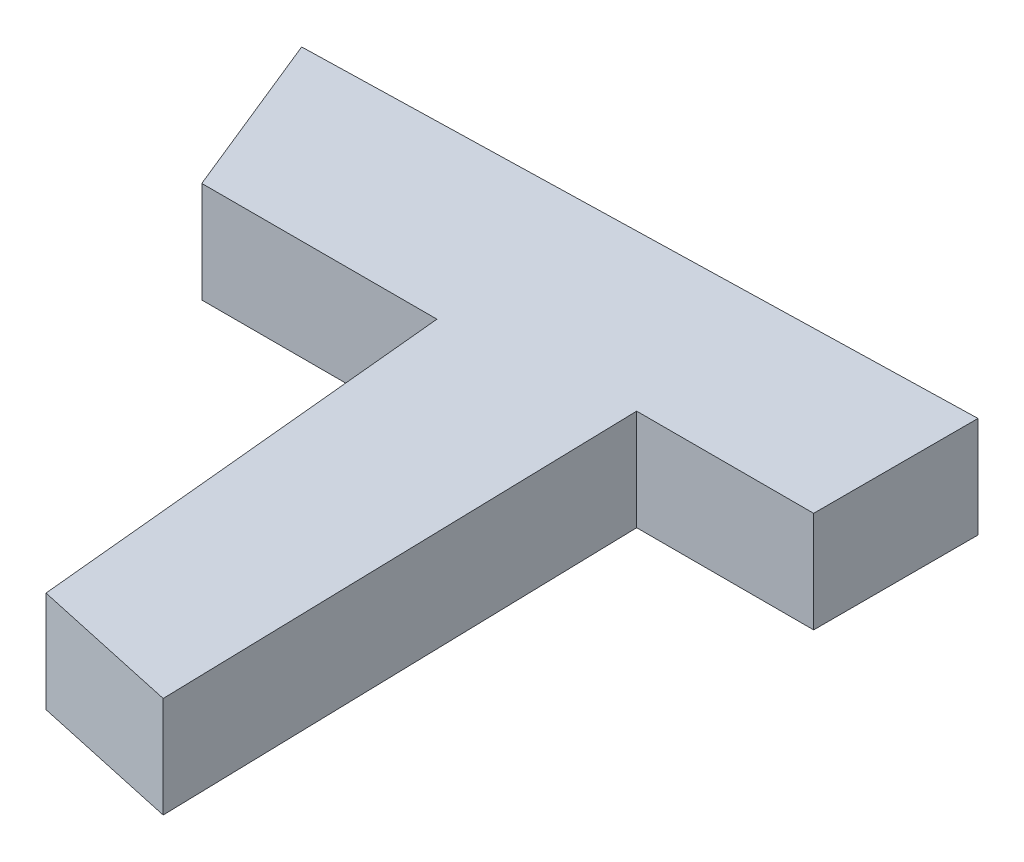
SolidWorks part; units mm, degrees
ref_plane "Front Plane" through (0, 0, 0) normal (0, 0, 1) x (1, 0, 0)
ref_plane "Top Plane" through (0, 0, 0) normal (0, 1, 0) x (1, 0, 0)
ref_plane "Right Plane" through (0, 0, 0) normal (1, 0, 0) x (0, 0, -1)
sketch "Sketch1" plane through (0, 0, 0) normal (0, 1, 0) x (1, 0, 0)
  line L0 (0, 0) -> (65.3512, 1.6275)
  line L1 (65.3512, 1.6275) -> (65.3512, -14.6477)
  line L2 (65.3512, -14.6477) -> (47.8241, -14.6477)
  line L3 (47.8241, -14.6477) -> (49.0217, -62.7359)
  line L4 (49.0217, -62.7359) -> (34.1775, -59.4951)
  line L5 (34.1775, -59.4951) -> (30.0465, -16.6508)
  line L6 (30.0465, -16.6508) -> (6.7605, -16.6508)
  line L7 (6.7605, -16.6508) -> (0, 0)
extrude "Boss-Extrude1" add sketch "Sketch1" along normal blind 10
